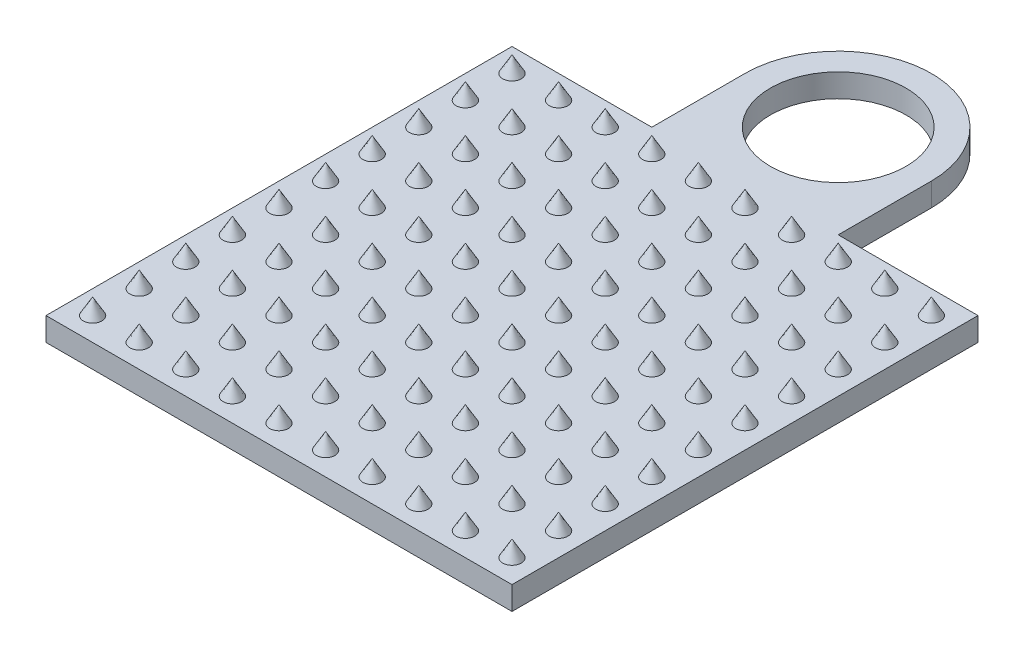
SolidWorks part; units mm, degrees
ref_plane "Front Plane" through (0, 0, 0) normal (0, 0, 1) x (1, 0, 0)
ref_plane "Top Plane" through (0, 0, 0) normal (0, 1, 0) x (1, 0, 0)
ref_plane "Right Plane" through (0, 0, 0) normal (1, 0, 0) x (0, 0, -1)
sketch "Sketch1" plane through (0, 0, 0) normal (0, 1, 0) x (1, 0, 0)
  line L1 (5, -5) -> (-5, -5)
  line L2 (5, -5) -> (5, 5)
  line L3 (5, 5) -> (-5, 5)
  line L4 (-5, -5) -> (-5, 5)
  line L5 (5, -5) -> (-5, 5) construction
  line L6 (5, 5) -> (-5, -5) construction
  point P0 (0, 0)
  dimension "D1" = 10
  dimension "D2" = 10
extrude "Plate" add sketch "Sketch1" along normal blind 0.5
sketch "Sketch2" plane through (0, 0.5, 0) normal (0, 1, 0) x (1, 0, 0)
  line L0 (-5, -5) -> (5, -5) construction
  line L1 (-5, 5) -> (-5, -5) construction
  circle A0 centre (-4.5, -4.5) radius 0.2
  dimension "D1" = 0.4
  dimension "D2" = 0.5
  dimension "D3" = 0.5
sketch "Sketch4" plane through (0, 0, 0) normal (0, 1, 0) x (1, 0, 0)
  line L5 (-2, 7) -> (-2, 5)
  line L6 (5, 5) -> (-5, 5) construction
  line L8 (-5, 5) -> (-5, -5) construction
  line L9 (-2, 5) -> (2, 5)
  line L10 (2, 5) -> (2, 7)
  arc A0 (-2, 7) -> (2, 7) centre (0, 7) cw
  point P0 (0, 7)
  dimension "D3" = 5
extrude "Boss-Extrude3" add sketch "Sketch4" along normal blind 0.5
sketch "Sketch5" plane through (0, 0.5, 0) normal (0, 1, 0) x (1, 0, 0)
  circle A0 centre (0, 7) radius 1.4559
extrude "Cut-Extrude1" cut sketch "Sketch5" against normal blind 1.5 and the other way blind 0.5
extrude "Cone" add sketch "Sketch2" along normal blind 10.25 draft 30
pattern_linear "LPattern1" count 10 spacing 1 along (1, 0, 0) count 10 spacing 1 along (0, 0, -1) of "Cone"
